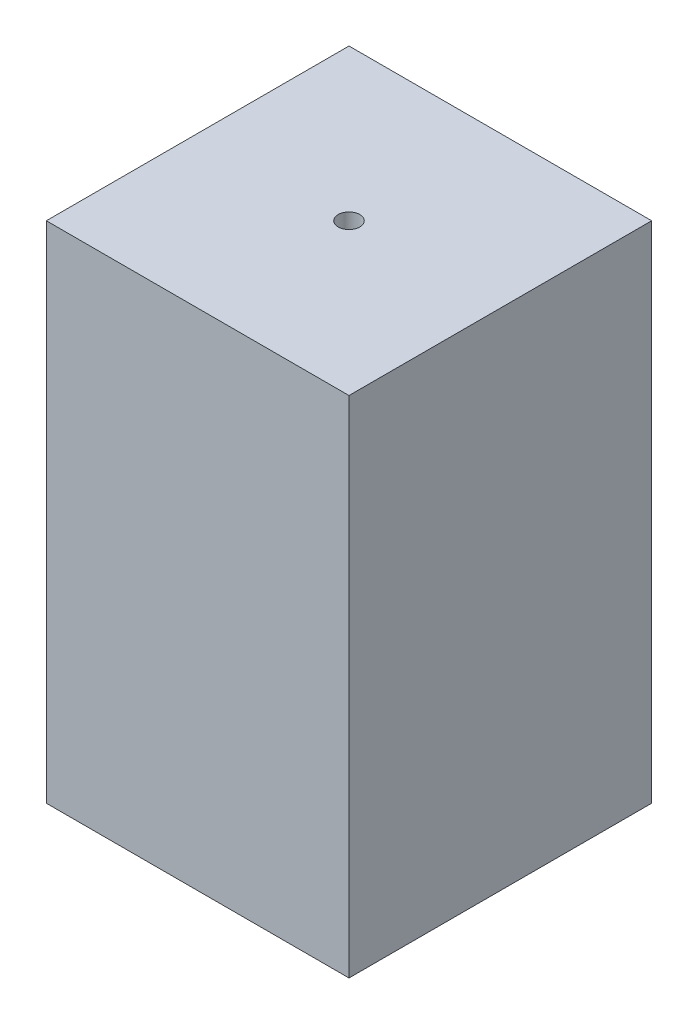
SolidWorks part; units mm, degrees
ref_plane "Front Plane" through (0, 0, 0) normal (0, 0, 1) x (1, 0, 0)
ref_plane "Top Plane" through (0, 0, 0) normal (0, 1, 0) x (1, 0, 0)
ref_plane "Right Plane" through (0, 0, 0) normal (1, 0, 0) x (0, 0, -1)
sketch "Sketch1" plane through (0, 0, 0) normal (0, 1, 0) x (1, 0, 0)
  line L1 (-60, 60) -> (60, 60)
  line L2 (-60, 60) -> (-60, -60)
  line L3 (-60, -60) -> (60, -60)
  line L4 (60, 60) -> (60, -60)
  line L5 (-60, 60) -> (60, -60) construction
  line L6 (-60, -60) -> (60, 60) construction
  circle A0 centre (0, 0) radius 4.2857
  point P0 (0, 0)
  dimension "D1" = 120
  dimension "D2" = 120
extrude "Boss-Extrude1" add sketch "Sketch1" along normal blind 10
sketch "Sketch2" plane through (0, 0, 0) normal (0, -1, 0) x (1, 0, 0)
  line L8 (50, -50) -> (50, 50)
  line L9 (50, 50) -> (-50, 50)
  line L10 (-50, 50) -> (-50, -50)
  line L11 (-50, -50) -> (50, -50)
  line L12 (50, -50) -> (50, 50)
  line L13 (50, 50) -> (-50, 50)
  line L14 (-50, 50) -> (-50, -50)
  line L15 (-50, -50) -> (50, -50)
  line L20 (60, -60) -> (60, 60)
  line L21 (60, 60) -> (-60, 60)
  line L22 (-60, 60) -> (-60, -60)
  line L23 (-60, -60) -> (60, -60)
  line L24 (60, -60) -> (60, 60)
  line L25 (60, 60) -> (-60, 60)
  line L26 (-60, 60) -> (-60, -60)
  line L27 (-60, -60) -> (60, -60)
  dimension "D1" = 10
  dimension "D2" = 0
extrude "Boss-Extrude2" add sketch "Sketch2" along normal blind 190
sketch "Sketch3" plane through (0, -190, 0) normal (0, -1, 0) x (1, 0, 0)
  line L0 (-60, 60) -> (-60, -60) construction
  line L1 (-60, -60) -> (60, -60) construction
  line L2 (60, 60) -> (-60, 60) construction
  line L3 (60, -60) -> (60, 60) construction
  circle A0 centre (-55, -55) radius 3.25
  circle A1 centre (55, 55) radius 3.25
  circle A2 centre (-55, 55) radius 3.25
  circle A3 centre (55, -55) radius 3.25
  dimension "D1" = 5
  dimension "D2" = 5
  dimension "D3" = 5
  dimension "D4" = 5
extrude "Cut-Extrude1" cut sketch "Sketch3" against normal blind 15
sketch "Sketch4" plane through (0, 0, -60) normal (0, 0, -1) x (-1, 0, 0)
  line L0 (60, -190) -> (-60, -190) construction
  line L1 (60, 10) -> (60, -190) construction
  circle A0 centre (0, -174.75) radius 6.5
  dimension "D1" = 13
  dimension "D2" = 15.25
  dimension "D3" = 60
extrude "Cut-Extrude2" cut sketch "Sketch4" against normal up to next
